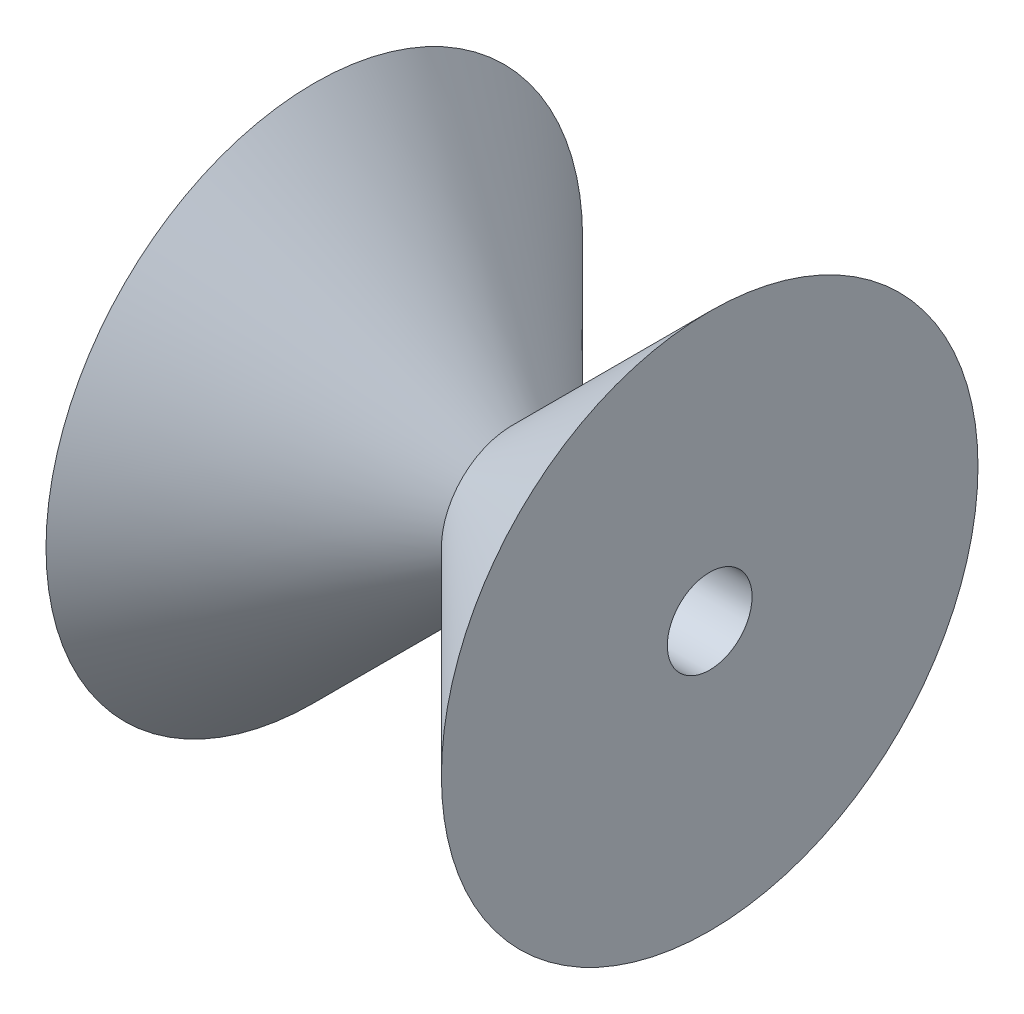
SolidWorks part; units mm, degrees
other "Spindle Wheel"
ref_plane "Front Plane" through (0, 0, 0) normal (0, 0, 1) x (1, 0, 0)
ref_plane "Top Plane" through (0, 0, 0) normal (0, 1, 0) x (1, 0, 0)
ref_plane "Right Plane" through (0, 0, 0) normal (1, 0, 0) x (0, 0, -1)
sketch "Sketch1" plane through (0, 0, 0) normal (1, 0, 0) x (0, 0, -1)
  circle A0 centre (0, 0) radius 12.5
  dimension "D1" = 25
extrude "Boss-Extrude1" add sketch "Sketch1" along normal blind 35 draft 45 draft outward yes
mirror "Mirror1" about plane through (0, 0, 0) normal (1, 0, 0) of "Boss-Extrude1"
sketch "Sketch2" plane through (35, 0, 0) normal (1, 0, 0) x (0, 0, -1)
  circle A0 centre (0, 0) radius 7.5
  dimension "D1" = 15
extrude "Support Arm Hole" cut sketch "Sketch2" against normal through all
